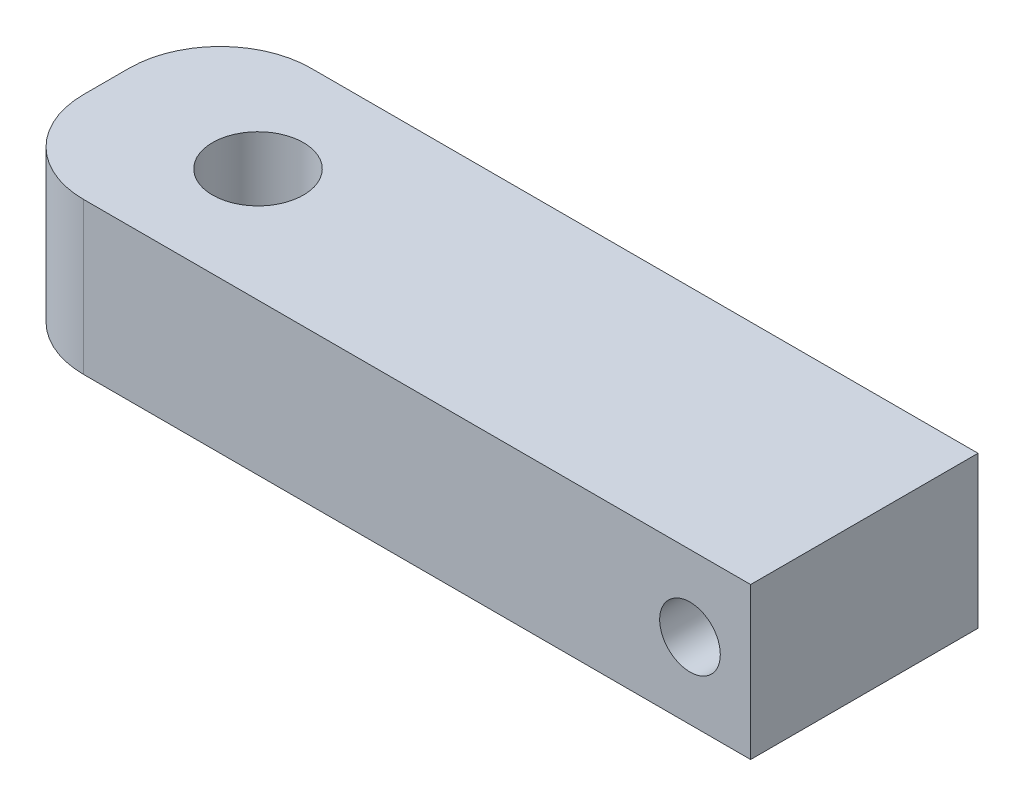
SolidWorks part; units mm, degrees
ref_plane "Front Plane" through (0, 0, 0) normal (0, 0, 1) x (1, 0, 0)
ref_plane "Top Plane" through (0, 0, 0) normal (0, 1, 0) x (1, 0, 0)
ref_plane "Right Plane" through (0, 0, 0) normal (1, 0, 0) x (0, 0, -1)
sketch "Sketch1" plane through (0, 0, 0) normal (0, 0, 1) x (1, 0, 0)
  line L1 (-31.75, 6.35) -> (31.75, 6.35)
  line L2 (-31.75, 6.35) -> (-31.75, -6.35)
  line L3 (-31.75, -6.35) -> (31.75, -6.35)
  line L4 (31.75, 6.35) -> (31.75, -6.35)
  circle A0 centre (26.67, 0) radius 2.54
  point P4 (31.75, 0)
  point P5 (0, 6.35)
  point P9 (0, 0)
  dimension "D3" = 5.08
  dimension "D1" = 63.5
  dimension "D2" = 12.7
  dimension "D4" = 5.08
extrude "Boss-Extrude1" add sketch "Sketch1" along normal blind 19.05
sketch "Sketch2" plane through (0, 6.35, 0) normal (0, 1, 0) x (1, 0, 0)
  line L1 (-31.75, -19.05) -> (-31.75, 0) construction
  circle A0 centre (-19.05, -9.525) radius 3.81
  point P8 (-31.75, -9.525)
  dimension "D2" = 7.62
  dimension "D1" = 12.7
extrude "Cut-Extrude1" cut sketch "Sketch2" against normal up to next
fillet "Fillet1" radius 7.62 2 edges at (-31.75, 0, 19.05) (-31.75, 0, 0)
